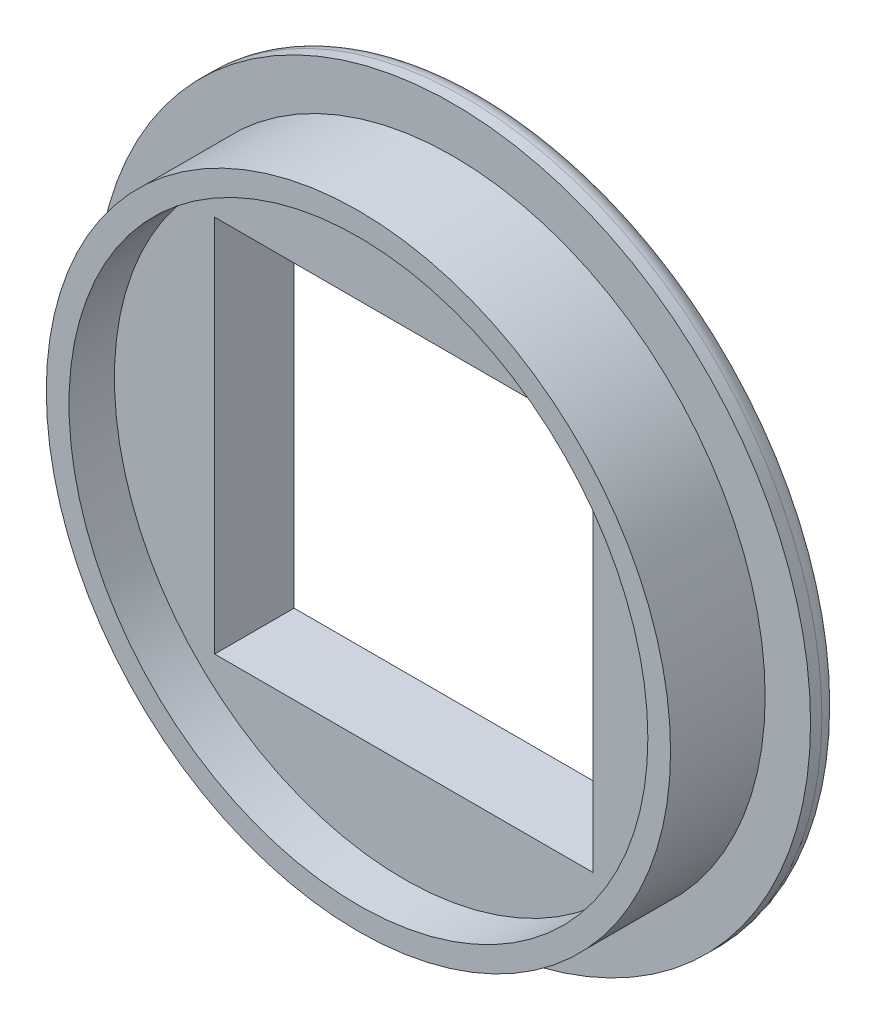
SolidWorks part; units mm, degrees
ref_plane "Front Plane" through (0, 0, 0) normal (0, 0, 1) x (1, 0, 0)
ref_plane "Top Plane" through (0, 0, 0) normal (0, 1, 0) x (1, 0, 0)
ref_plane "Right Plane" through (0, 0, 0) normal (1, 0, 0) x (0, 0, -1)
sketch "Sketch2" plane through (0, 0, 0) normal (0, 0, 1) x (1, 0, 0)
  line L1 (-5, -5) -> (5, -5)
  line L2 (-5, -5) -> (-5, 5)
  line L3 (-5, 5) -> (5, 5)
  line L4 (5, -5) -> (5, 5)
  line L5 (-5, -5) -> (5, 5) construction
  line L6 (-5, 5) -> (5, -5) construction
  circle A0 centre (0, 0) radius 8.25
  dimension "D1" = 16.5
  dimension "D2" = 10
extrude "Boss-Extrude1" add sketch "Sketch2" along normal blind 3.3
sketch "Sketch3" plane through (0, 0, 0) normal (0, 0, -1) x (-1, 0, 0)
  line L0 (5, -5) -> (-5, -5) construction
  line L1 (-5, -5) -> (-5, 5) construction
  line L2 (5, 5) -> (5, -5) construction
  line L3 (-5, 5) -> (5, 5) construction
  line L4 (5, -5) -> (-5, -5)
  line L5 (-5, -5) -> (-5, 5)
  line L6 (5, 5) -> (5, -5)
  line L7 (-5, 5) -> (5, 5)
  circle A0 centre (0, 0) radius 9.45
  dimension "D1" = 18.9
extrude "Boss-Extrude2" add sketch "Sketch3" against normal offset from surface (0.8 mm away) 2.5 up to face at (8.25, 0, 3.3)
sketch "Sketch4" plane through (0, 0, 3.3) normal (0, 0, 1) x (1, 0, 0)
  circle A0 centre (0, 0) radius 7.65
  dimension "D1" = 15.3
extrude "Cut-Extrude1" cut sketch "Sketch4" against normal blind 1.2
fillet "Fillet1" radius 0.5 1 edges at (-9.45, 0, 0)
